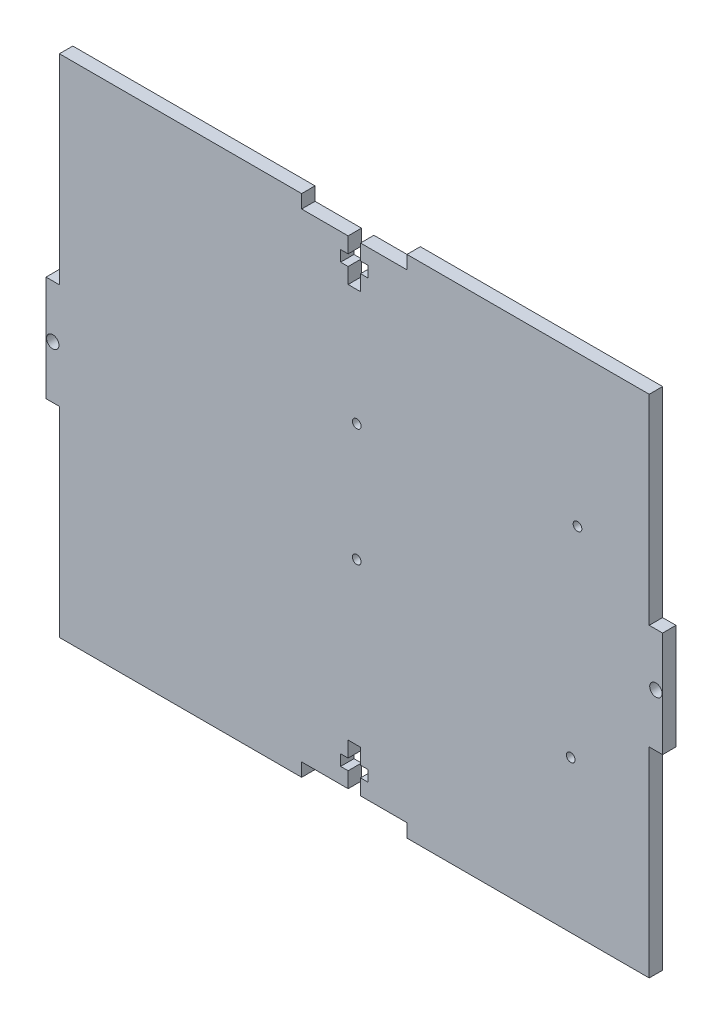
SolidWorks part; units mm, degrees
ref_plane "Front Plane" through (0, 0, 0) normal (0, 0, 1) x (1, 0, 0)
ref_plane "Top Plane" through (0, 0, 0) normal (0, 1, 0) x (1, 0, 0)
ref_plane "Right Plane" through (0, 0, 0) normal (1, 0, 0) x (0, 0, -1)
sketch "Sketch1" plane through (0, 0, 0) normal (0, 0, 1) x (1, 0, 0)
  line L0 (0, 60) -> (0, -60) construction
  line L1 (-70, 60) -> (70, 60)
  line L2 (-70, 60) -> (-70, -60)
  line L3 (-70, -60) -> (70, -60)
  line L4 (70, 60) -> (70, -60)
  line L5 (-70, 60) -> (70, -60) construction
  line L6 (-70, -60) -> (70, 60) construction
  line L7 (-70, 0) -> (70, 0) construction
  line L8 (-3.25, -50.525) -> (3.25, -50.525)
  line L9 (12.5, 60) -> (-12.5, 60)
  line L10 (12.5, 60) -> (12.5, 56.825)
  line L11 (12.5, 56.825) -> (-12.5, 56.825)
  line L12 (-12.5, 60) -> (-12.5, 56.825)
  line L13 (12.5, 60) -> (-12.5, 56.825) construction
  line L14 (12.5, 56.825) -> (-12.5, 60) construction
  line L15 (-1.47, 56.825) -> (1.47, 56.825)
  line L16 (-1.47, 56.825) -> (-1.47, 46.825)
  line L17 (-1.47, 46.825) -> (1.47, 46.825)
  line L18 (1.47, 56.825) -> (1.47, 46.825)
  line L19 (-1.47, 56.825) -> (1.47, 46.825) construction
  line L20 (-1.47, 46.825) -> (1.47, 56.825) construction
  line L21 (-3.25, 53.125) -> (3.25, 53.125)
  line L22 (-3.25, 53.125) -> (-3.25, 50.525)
  line L23 (-3.25, 50.525) -> (3.25, 50.525)
  line L24 (3.25, 53.125) -> (3.25, 50.525)
  line L25 (-3.25, 53.125) -> (3.25, 50.525) construction
  line L26 (-3.25, 50.525) -> (3.25, 53.125) construction
  line L27 (3.25, -53.125) -> (3.25, -50.525)
  line L28 (-3.25, -53.125) -> (3.25, -53.125)
  line L29 (-3.25, -53.125) -> (-3.25, -50.525)
  line L30 (-1.47, -46.825) -> (1.47, -46.825)
  line L31 (1.47, -56.825) -> (1.47, -46.825)
  line L32 (-1.47, -56.825) -> (1.47, -56.825)
  line L33 (-1.47, -56.825) -> (-1.47, -46.825)
  line L34 (12.5, -56.825) -> (-12.5, -56.825)
  line L35 (-12.5, -60) -> (-12.5, -56.825)
  line L36 (12.5, -60) -> (-12.5, -60)
  line L37 (12.5, -60) -> (12.5, -56.825)
  line L38 (73.175, -12.5) -> (70, -12.5)
  line L39 (-73.175, 12.5) -> (-70, 12.5)
  line L40 (-73.175, 12.5) -> (-73.175, -12.5)
  line L41 (-73.175, -12.5) -> (-70, -12.5)
  line L42 (-70, 12.5) -> (-70, -12.5)
  line L43 (-73.175, 12.5) -> (-70, -12.5) construction
  line L44 (-73.175, -12.5) -> (-70, 12.5) construction
  line L45 (70, 12.5) -> (70, -12.5)
  line L46 (73.175, 12.5) -> (70, 12.5)
  line L47 (73.175, 12.5) -> (73.175, -12.5)
  circle A0 centre (-71.5875, 0) radius 1.47
  circle A1 centre (71.5875, 0) radius 1.47
  point P0 (0, 0)
  point P10 (0, 58.4125)
  point P15 (0, 51.825)
  point P20 (0, 51.825)
  point P37 (-71.5875, 0)
  dimension "D11" = 2.94
  dimension "D1" = 120
  dimension "D2" = 140
  dimension "D3" = 3.175
  dimension "D4" = 10
  dimension "D5" = 2.94
  dimension "D6" = 25
  dimension "D7" = 6.5
  dimension "D8" = 2.6
  dimension "D9" = 6.3
  dimension "D10" = 3.175
extrude "Boss-Extrude1" add sketch "Sketch1" along normal mid plane 3.175 contours L21 L24 L23 L18 L17 L16 L22 L11 L12 L1 L2 L3 L4 L10 | L40 L39 L42 L41 | A0 | L38 L45 L46 L47 | A1
sketch "Sketch3" plane through (0, 0, -1.5875) normal (0, 0, -1) x (-1, 0, 0)
  circle A0 centre (-51.375, -23.975) radius 1.0287 construction
  circle A1 centre (-52.975, 24.325) radius 1.0287 construction
  circle A2 centre (-0.575, -8.675) radius 1.0287 construction
  circle A3 centre (-0.575, 19.225) radius 1.0287 construction
  circle A4 centre (-51.375, -23.975) radius 1.0287
  circle A5 centre (-52.975, 24.325) radius 1.0287
  circle A6 centre (-0.575, -8.675) radius 1.0287
  circle A7 centre (-0.575, 19.225) radius 1.0287
extrude "Cut-Extrude1" cut sketch "Sketch3" against normal through all
